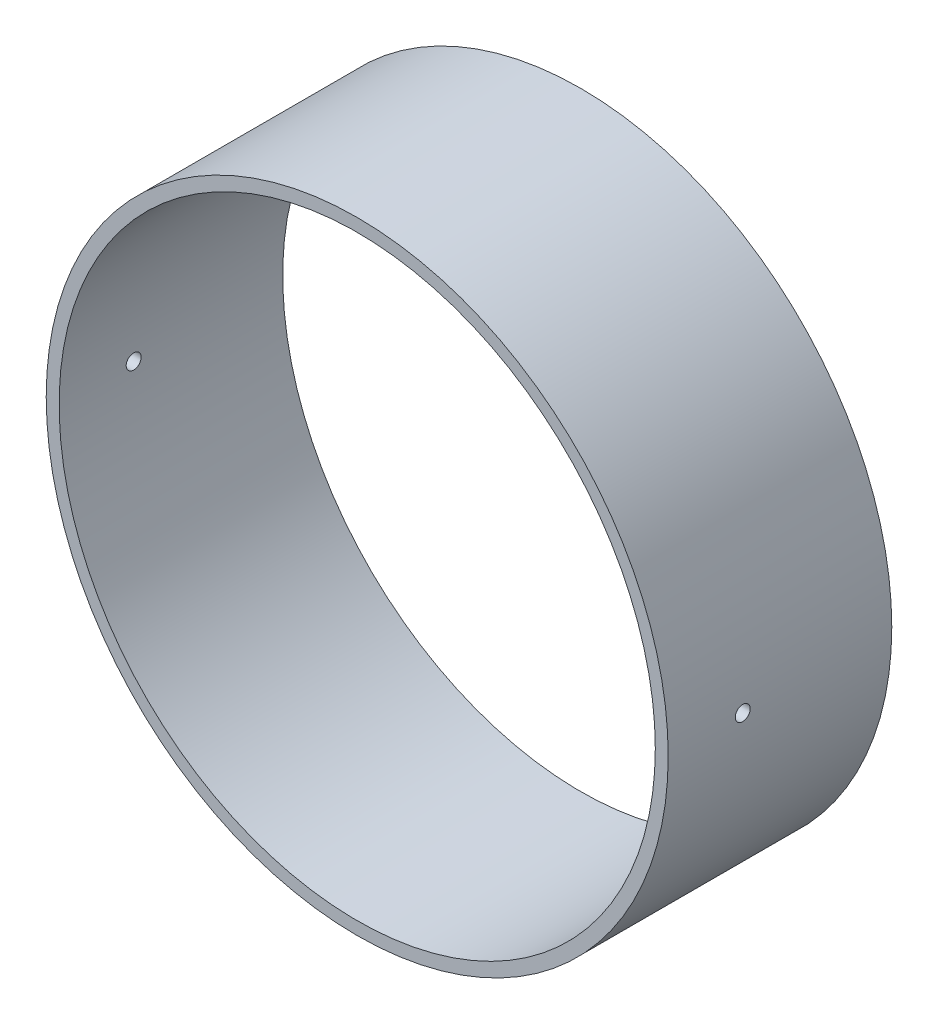
SolidWorks part; units mm, degrees
material "Silicon Dioxide"
ref_plane "Front Plane" through (0, 0, 0) normal (0, 0, 1) x (1, 0, 0)
ref_plane "Top Plane" through (0, 0, 0) normal (0, 1, 0) x (1, 0, 0)
ref_plane "Right Plane" through (0, 0, 0) normal (1, 0, 0) x (0, 0, -1)
sketch "Sketch1" plane through (0, 0, 0) normal (0, 0, 1) x (1, 0, 0)
  circle A0 centre (0, 0) radius 38.1
  circle A1 centre (0, 0) radius 39.75
  dimension "D1" = 76.2
  dimension "D2" = 79.5
extrude "Boss-Extrude1" add sketch "Sketch1" along normal blind 28.575
ref_plane "Plane1" through (-39.75, 0, 0) normal (-1, 0, 0) x (0, 0, 1)
sketch "Sketch2" plane through (-39.75, 0, 0) normal (-1, 0, 0) x (0, 0, 1)
  line L0 (0, 39.75) -> (0, -39.75) construction
  circle A0 centre (19.05, 0) radius 0.9525
  dimension "D1" = 1.905
  dimension "D2" = 19.05
extrude "Cut-Extrude1" cut sketch "Sketch2" against normal through all contours A0
